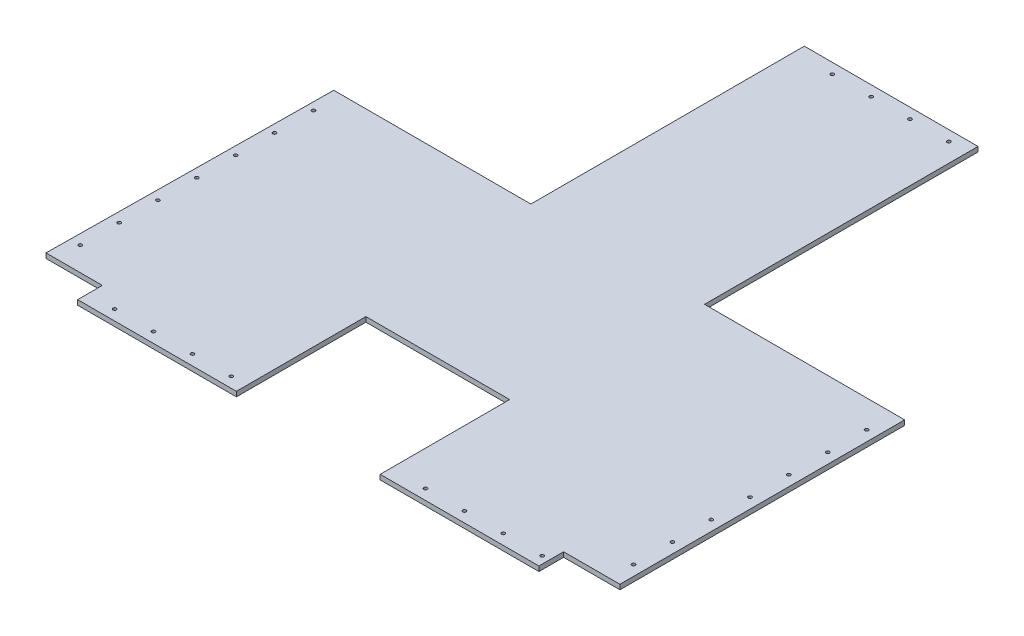
SolidWorks part; units mm, degrees
ref_plane "Front Plane" through (0, 0, 0) normal (0, 0, 1) x (1, 0, 0)
ref_plane "Top Plane" through (0, 0, 0) normal (0, 1, 0) x (1, 0, 0)
ref_plane "Right Plane" through (0, 0, 0) normal (1, 0, 0) x (0, 0, -1)
sketch "Sketch1" plane through (0, 329.9257, 0) normal (0, 1, 0) x (1, 0, 0)
  line L1 (180.8999, -210.7827) -> (180.8999, 70.7173)
  line L5 (180.8999, 70.7173) -> (359.6999, 70.7173)
  line L7 (359.6999, 70.7173) -> (359.6999, -210.7827)
  line L8 (359.6999, -210.7827) -> (565.6999, -210.7827)
  line L9 (565.6999, -210.7827) -> (565.6999, -503.8827)
  line L10 (565.6999, -503.8827) -> (570.6999, -503.8827) construction
  line L12 (540.2999, -529.2827) -> (0.2999, -529.2827) construction
  line L13 (510.6999, -529.2827) -> (29.8999, -529.2827) construction
  line L14 (344.2999, -396.0177) -> (196.2999, -396.0177)
  line L15 (196.2999, -396.0177) -> (196.2999, -529.2827)
  line L16 (196.2999, -529.2827) -> (32.8749, -529.2827)
  line L17 (32.8749, -529.2827) -> (32.8749, -503.8827)
  line L18 (32.8749, -503.8827) -> (-25.1001, -503.8827)
  line L19 (-25.1001, -503.8827) -> (-21.9251, -210.7827)
  line L20 (344.2999, -529.2827) -> (344.2999, -396.0177)
  line L21 (340.2999, -465.0177) -> (344.2999, -465.0177) construction
  line L22 (340.2999, -530.0177) -> (340.2999, -400.0177) construction
  line L23 (200.2999, -465.0177) -> (196.2999, -465.0177) construction
  line L24 (200.2999, -400.0177) -> (200.2999, -530.0177) construction
  line L25 (270.2999, -396.0177) -> (270.2999, -400.0177) construction
  line L26 (340.2999, -400.0177) -> (200.2999, -400.0177) construction
  line L27 (565.6999, -529.2827) -> (565.6999, 70.7173) construction
  line L28 (344.2999, -529.2827) -> (507.7249, -529.2827)
  line L29 (507.7249, -529.2827) -> (507.7249, -503.8827)
  line L30 (540.2999, -503.8827) -> (0.2999, -503.8827) construction
  line L31 (507.7249, -503.8827) -> (565.6999, -503.8827)
  line L32 (-21.9251, -210.7827) -> (180.8999, -210.7827)
  line L34 (79.4874, -210.7827) -> (79.4874, -206.7827) construction
  line L35 (562.5249, -206.7827) -> (-21.9251, -206.7827) construction
  line L36 (180.8999, -70.0327) -> (176.8999, -70.0327) construction
  line L37 (176.8999, -206.4827) -> (176.8999, 70.7173) construction
  line L38 (359.6999, -70.0327) -> (363.6999, -70.0327) construction
  line L39 (363.6999, -206.4827) -> (363.6999, 70.7173) construction
  line L40 (-21.9251, -223.9327) -> (-21.9251, -207.7827) construction
  line L41 (510.6999, 70.7173) -> (29.8999, 70.7173) construction
  dimension "D1" = 4
extrude "Boss-Extrude1" add sketch "Sketch1" along normal blind 5
sketch "Sketch2" plane through (0, 329.9257, 0) normal (0, -1, 0) x (1, 0, 0)
  circle A0 centre (60.2999, 518.6077) radius 1.75
  circle A1 centre (380.2999, 518.6077) radius 1.75
  circle A2 centre (220.2999, -60.0423) radius 1.75
  circle A3 centre (100.2999, 518.6077) radius 1.75
  circle A4 centre (420.2999, 518.6077) radius 1.75
  circle A5 centre (260.2999, -60.0423) radius 1.75
  circle A6 centre (140.2999, 518.6077) radius 1.75
  circle A7 centre (460.2999, 518.6077) radius 1.75
  circle A8 centre (300.2999, -60.0423) radius 1.75
  circle A9 centre (180.2999, 518.6077) radius 1.75
  circle A10 centre (500.2999, 518.6077) radius 1.75
  circle A11 centre (340.2999, -60.0423) radius 1.75
  circle A12 centre (-14.4251, 239.2827) radius 1.75
  circle A13 centre (555.0249, 239.2827) radius 1.75
  circle A14 centre (-14.4251, 279.2827) radius 1.75
  circle A15 centre (555.0249, 279.2827) radius 1.75
  circle A16 centre (-14.4251, 319.2827) radius 1.75
  circle A17 centre (555.0249, 319.2827) radius 1.75
  circle A18 centre (-14.4251, 359.2827) radius 1.75
  circle A19 centre (555.0249, 359.2827) radius 1.75
  circle A20 centre (-14.4251, 399.2827) radius 1.75
  circle A21 centre (555.0249, 399.2827) radius 1.75
  circle A22 centre (-14.4251, 439.2827) radius 1.75
  circle A23 centre (555.0249, 439.2827) radius 1.75
  circle A24 centre (-14.4251, 479.2827) radius 1.75
  circle A25 centre (555.0249, 479.2827) radius 1.75
  dimension "D1" = 3.5
  dimension "D3" = 40
  dimension "D4" = 3.5
  dimension "D6" = 40
  dimension "D2" = 4
  dimension "D5" = 7
extrude "Cut-Extrude1" cut sketch "Sketch2" against normal through all
